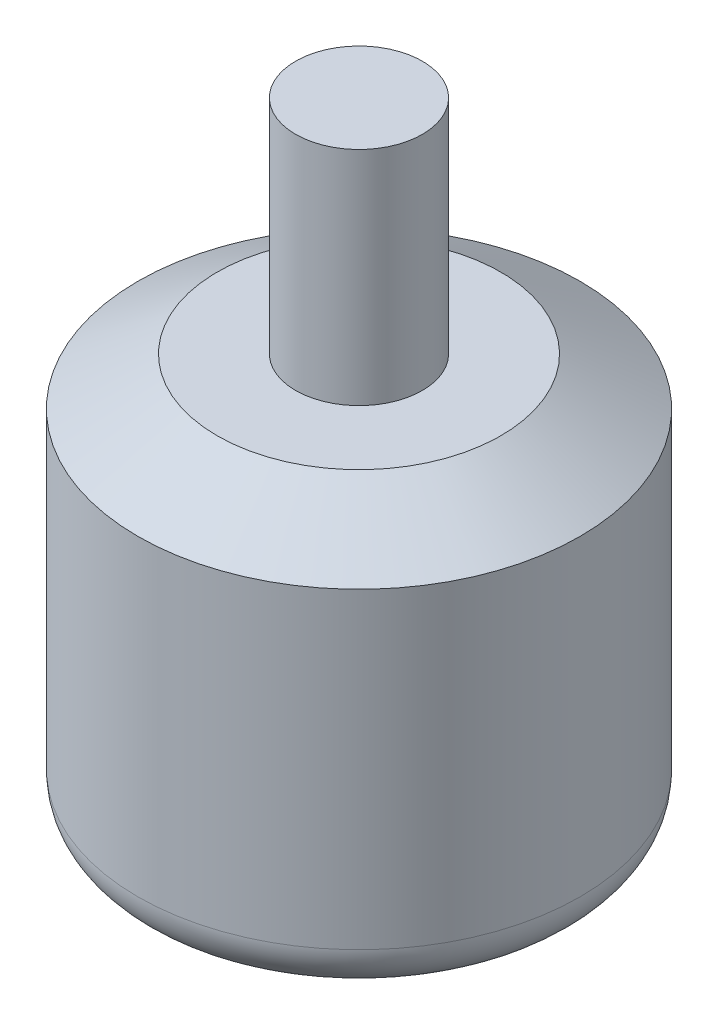
SolidWorks part; units mm, degrees
material "Copper"
ref_plane "Front Plane" through (0, 0, 0) normal (0, 0, 1) x (1, 0, 0)
ref_plane "Top Plane" through (0, 0, 0) normal (0, 1, 0) x (1, 0, 0)
ref_plane "Right Plane" through (0, 0, 0) normal (1, 0, 0) x (0, 0, -1)
sketch "Sketch1" plane through (0, 0, 0) normal (0, 1, 0) x (1, 0, 0)
  circle A0 centre (0, 0) radius 13.95
  dimension "D1" = 27.9
extrude "Boss-Extrude1" add sketch "Sketch1" along normal blind 25.7
chamfer "Chamfer1" distance 3 distance2 5 1 edges at (0, 25.7, 13.95)
sketch "Sketch2" plane through (0, 25.7, 0) normal (0, 1, 0) x (1, 0, 0)
  circle A0 centre (0, 0) radius 4
extrude "Boss-Extrude2" add sketch "Sketch2" along normal blind 14
hole_wizard "M3x0.5 Tapped Hole1" positions "Sketch4" profile "Sketch3" tap size "M3x0.5" standard "ANSI Metric"
sketch "Sketch4" plane through (0, 0, 0) normal (0, -1, 0) x (-1, 0, 0)
  line L0 (0, 8) -> (0, -8) construction
  line L1 (-9.5, 0) -> (9.5, 0) construction
  point P6 (0, 8)
  point P7 (0, -8)
  point P9 (-9.5, 0)
  point P10 (9.5, 0)
  point P24 (0, 0)
  point P25 (0, 0)
  dimension "D1" = 16
  dimension "D2" = 19
sketch "Sketch3" plane through (0, 0, -8) normal (1, 0, 0) x (0, 0, -1)
  line L0 (0, 0) -> (0, 8.2511)
  line L1 (0, 8.2511) -> (1.25, 7.5)
  line L2 (1.25, 7.5) -> (1.25, 0)
  line L5 (1.25, 0) -> (0, 0)
  line L10 (0, 8.2511) -> (-1.25, 7.5) construction
  line L11 (0, -6.35) -> (0, 107.95) construction
  dimension "Tap Drill Dia." = 2.5
  dimension "Tap Drill Depth" = 7.5
  dimension "Drill Angle" = 118
cosmetic thread "Hole Thread1" parameters "D1"=6, "D2"=3
cosmetic thread "Hole Thread2" parameters "D1"=6, "D2"=3
cosmetic thread "Hole Thread3" parameters "D1"=6, "D2"=3
cosmetic thread "Hole Thread4" parameters "D1"=6, "D2"=3
fillet "Fillet1" radius 3 1 edges at (0, 0, 13.95)
sketch "Sketch5" plane through (0, 0, 0) normal (0, -1, 0) x (1, 0, 0)
  circle A0 centre (0, 0) radius 3
extrude "Boss-Extrude3" add sketch "Sketch5" along normal blind 2.5
sketch "Sketch6" plane through (0, 39.7, 0) normal (0, 1, 0) x (1, 0, 0)
  circle A0 centre (0, 0) radius 127
  dimension "D1" = 254
